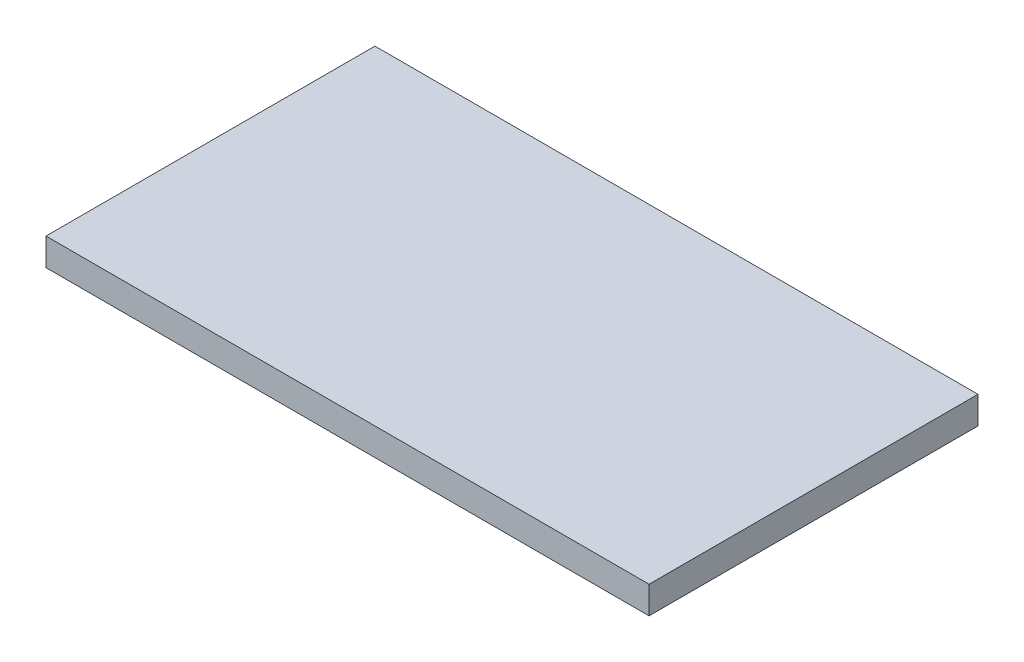
SolidWorks part; units mm, degrees
ref_plane "Ebene vorne" through (0, 0, 0) normal (0, 0, 1) x (1, 0, 0)
ref_plane "Ebene oben" through (0, 0, 0) normal (0, 1, 0) x (1, 0, 0)
ref_plane "Ebene rechts" through (0, 0, 0) normal (1, 0, 0) x (0, 0, -1)
sketch "Sketch1" plane through (0, 0, 0) normal (0, 1, 0) x (1, 0, 0)
  line L1 (-22, 12) -> (0, 12)
  line L2 (-22, 12) -> (-22, 0)
  line L3 (-22, 0) -> (0, 0)
  line L4 (0, 12) -> (0, 0)
  dimension "D1" = 12
  dimension "D2" = 22
extrude "Boss-Extrude1" add sketch "Sketch1" along normal blind 1 contours L2 L1 L4 L3
